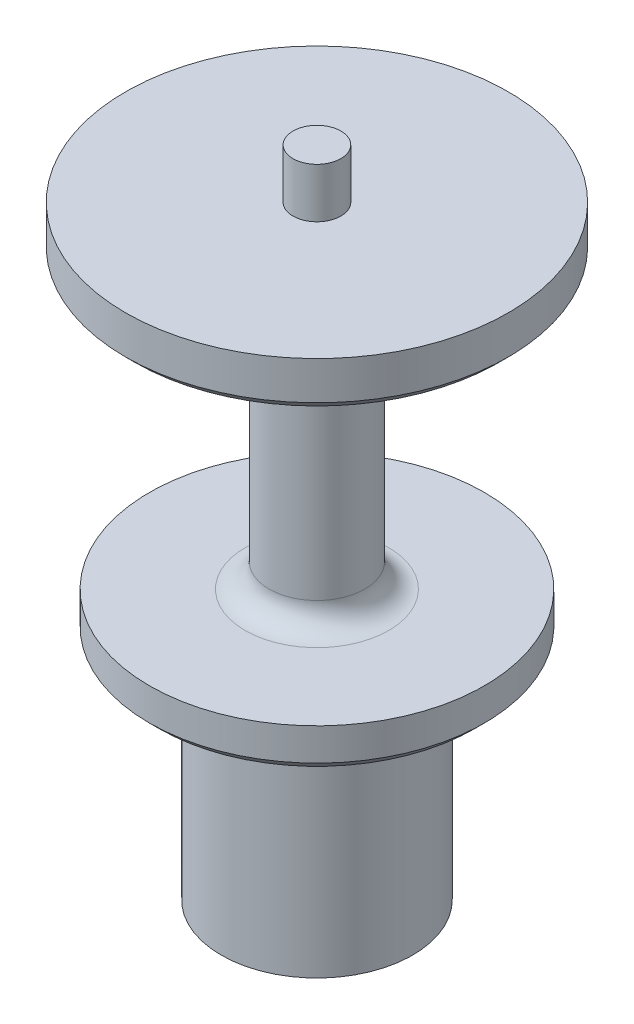
SolidWorks part; units mm, degrees
material "6061 Alloy"
ref_plane "Front Plane" through (0, 0, 0) normal (0, 0, 1) x (1, 0, 0)
ref_plane "Top Plane" through (0, 0, 0) normal (0, 1, 0) x (1, 0, 0)
ref_plane "Right Plane" through (0, 0, 0) normal (1, 0, 0) x (0, 0, -1)
sketch "Sketch1" plane through (0, 0, 0) normal (0, 1, 0) x (1, 0, 0)
  circle A0 centre (0, 0) radius 12.7
  dimension "D1" = 25.4
extrude "Boss-Extrude1" add sketch "Sketch1" along normal blind 30.1625
sketch "Sketch4" plane through (0, 30.1625, 0) normal (0, 1, 0) x (1, 0, 0)
  circle A0 centre (0, 0) radius 25.4
  dimension "D1" = 50.8
extrude "Boss-Extrude2" add sketch "Sketch4" along normal blind 50.0062 contours A0
sketch "Sketch2" plane through (0, 0, 0) normal (0, -1, 0) x (1, 0, 0)
  line L0 (-8.777, 1.1225) -> (-1.1225, 8.777)
  line L1 (-5.4125, -7) -> (5.4125, -7)
  line L2 (-7, -5.4125) -> (-7, 5.4125)
  line L3 (-5.4125, 7) -> (5.4125, 7)
  line L4 (7, -5.4125) -> (7, 5.4125)
  line L5 (-7, -7) -> (7, 7) construction
  line L6 (-7, 7) -> (7, -7) construction
  line L7 (-8.777, -1.1225) -> (-1.1225, -8.777)
  line L8 (1.1225, 8.777) -> (8.777, 1.1225)
  line L9 (1.1225, -8.777) -> (8.777, -1.1225)
  line L10 (-9.8995, 0) -> (9.8995, 0) construction
  line L11 (0, 9.8995) -> (0, -9.8995) construction
  circle A0 centre (0, 0) radius 9 construction
  arc A1 (-8.777, 1.1225) -> (-8.777, -1.1225) centre (-7.6544, 0) ccw
  arc A2 (-7, -5.4125) -> (-5.4125, -7) centre (-5.4125, -5.4125) ccw
  arc A3 (-1.1225, -8.777) -> (1.1225, -8.777) centre (0, -7.6544) ccw
  arc A4 (5.4125, -7) -> (7, -5.4125) centre (5.4125, -5.4125) ccw
  arc A5 (8.777, -1.1225) -> (8.777, 1.1225) centre (7.6544, 0) ccw
  arc A6 (7, 5.4125) -> (5.4125, 7) centre (5.4125, 5.4125) ccw
  arc A7 (1.1225, 8.777) -> (-1.1225, 8.777) centre (0, 7.6544) ccw
  arc A8 (-5.4125, 7) -> (-7, 5.4125) centre (-5.4125, 5.4125) ccw
  point P0 (0, 0)
  point P7 (0, 0)
  dimension "D2" = 18
  dimension "D3" = 1.5875
  dimension "D1" = 14
extrude "Cut-Extrude1" cut sketch "Sketch2" against normal blind 11.176 contours L0 A1 L7 L2 | L1 L9 L4 L8 L3 L0 L2 L7 | L3 A8 L2 L0 | L8 A7 L0 L3 | L4 A6 L3 L8 | L9 A5 L8 L4 | L1 A4 L4 L9 | L7 A3 L9 L1 | L2 A2 L1 L7
sketch "Sketch3" plane through (0, 11.176, 0) normal (0, -1, 0) x (1, 0, 0)
  circle A0 centre (0, 0) radius 6
  dimension "D1" = 12
extrude "Cut-Extrude2" cut sketch "Sketch3" against normal blind 8
sketch "Sketch5" plane through (0, 80.1688, 0) normal (0, 1, 0) x (1, 0, 0)
  circle A0 centre (0, 0) radius 3.175
  dimension "D1" = 6.35
extrude "Boss-Extrude3" add sketch "Sketch5" along normal blind 6.604
hole_wizard "#8-32 Tapped Hole1" [suppressed] positions "Sketch6" profile "Sketch8" tap size "#8-32" standard "ANSI Inch"
sketch "Sketch6" plane through (0, 87.5665, 0) normal (0, 1, 0) x (1, 0, 0)
  point P0 (0, 0)
sketch "Sketch8" plane through (0, 87.5665, 0) normal (1, 0, 0) x (0, 0, 1)
  line L0 (0, 0) -> (0, 87.5665)
  line L1 (0, 87.5665) -> (1.7272, 87.5665)
  line L2 (1.7272, 87.5665) -> (1.7272, 0)
  line L5 (1.7272, 0) -> (0, 0)
  line L11 (0, -6.35) -> (0, 107.95) construction
  dimension "Thru Tap Drill Dia." = 3.4544
  dimension "Thru Tap Drill Depth" = 87.5665
cosmetic thread "Hole Thread1" [suppressed] parameters "D2"=4.1656
sketch "Sketch9" plane through (0, 80.1688, 0) normal (0, 1, 0) x (1, 0, 0)
  circle A0 centre (0, 0) radius 25.4 construction
  circle A1 centre (0, 0) radius 25.4
  circle A2 centre (0, 0) radius 6.35
  dimension "D1" = 12.7
extrude "Cut-Extrude3" cut sketch "Sketch9" against normal blind 38.1 from offset 6.35 offset against normal yes
sketch "Sketch10" plane through (0, 30.1625, 0) normal (0, -1, 0) x (1, 0, 0)
  circle A0 centre (0, 0) radius 25.4 construction
  circle A1 centre (0, 0) radius 25.4
  circle A2 centre (0, 0) radius 22.225
  dimension "D1" = 44.45
extrude "Cut-Extrude4" cut sketch "Sketch10" against normal up to next
fillet "Fillet1" radius 3.175 2 edges at (0, 73.8188, 6.35) (0, 35.7188, 6.35)
chamfer "Chamfer1" distance 1.27 angle 45 2 edges at (0, 73.8188, 25.4) (0, 30.1625, -22.225)
